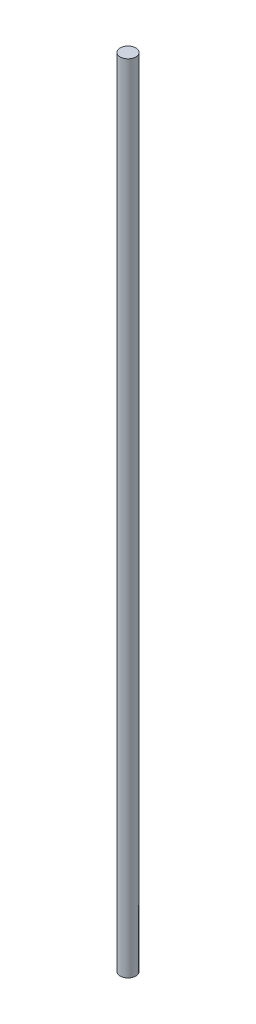
SolidWorks part; units mm, degrees
material "1060 Alloy"
ref_plane "Front Plane" through (0, 0, 0) normal (0, 0, 1) x (1, 0, 0)
ref_plane "Top Plane" through (0, 0, 0) normal (0, 1, 0) x (1, 0, 0)
ref_plane "Right Plane" through (0, 0, 0) normal (1, 0, 0) x (0, 0, -1)
sketch "Sketch1" plane through (0, 0, 0) normal (0, 1, 0) x (1, 0, 0)
  circle A0 centre (0, 0) radius 5
  dimension "D1" = 10
extrude "Boss-Extrude1" add sketch "Sketch1" along normal blind 506.5
equation "\"D1@Boss-Extrude1\"=450+59-2.5"
